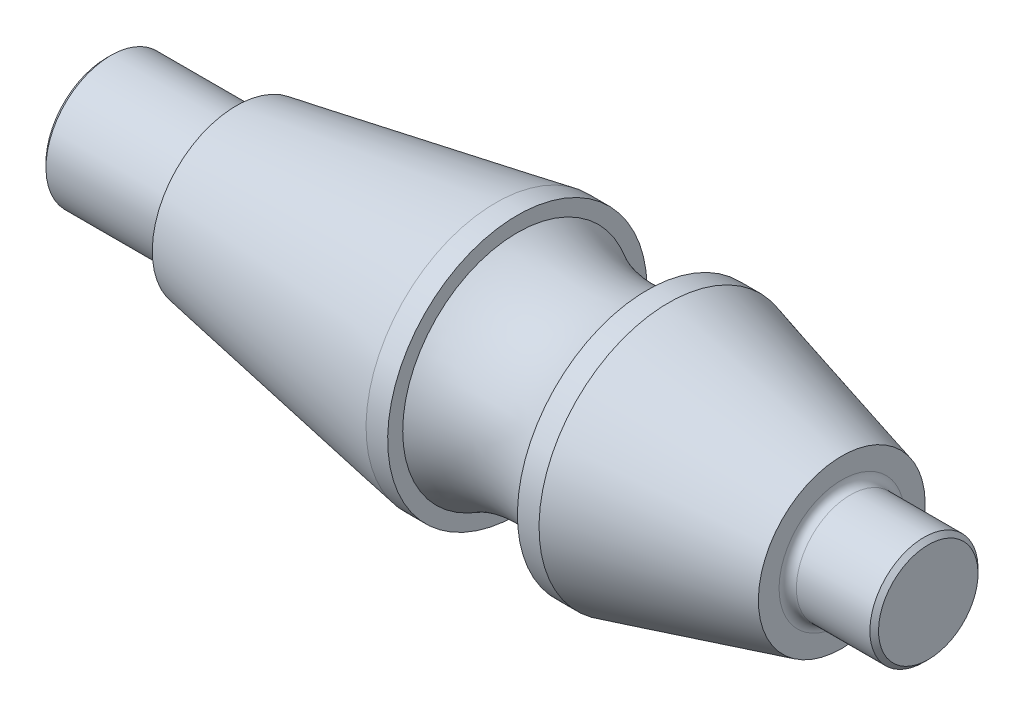
SolidWorks part; units mm, degrees
material "AISI 1045 Aço, trefilado"
ref_plane "Plano frontal" through (0, 0, 0) normal (0, 0, 1) x (1, 0, 0)
ref_plane "Plano superior" through (0, 0, 0) normal (0, 1, 0) x (1, 0, 0)
ref_plane "Plano direito" through (0, 0, 0) normal (1, 0, 0) x (0, 0, -1)
sketch "Esboço1" plane through (0, 0, 0) normal (0, 0, 1) x (1, 0, 0)
  line L0 (-95, 0) -> (95, 0) construction
  line L1 (-95, 0) -> (-95, 15)
  line L2 (-95, 15) -> (-65, 15)
  line L3 (-65, 15) -> (-65, 19.4204)
  line L4 (-65, 19.4204) -> (-5, 30)
  line L5 (-5, 30) -> (0, 30)
  line L6 (35, 30) -> (75, 19.282)
  line L7 (75, 19.282) -> (75, 12.5)
  line L8 (75, 12.5) -> (95, 12.5)
  line L9 (95, 12.5) -> (95, 0)
  line L10 (0, 30) -> (0, 26.5192)
  line L11 (30, 30) -> (30, 26.5192)
  line L12 (30, 30) -> (35, 30)
  line L13 (-95, 0) -> (95, 0)
  arc A0 (0, 26.5192) -> (30, 26.5192) centre (15, 52.5) ccw
  point P2 (0, 0)
  point P17 (0, 0)
  dimension "D11" = 45
  dimension "D12" = 30
  dimension "D1" = 190
  dimension "D2" = 30
  dimension "D3" = 25
  dimension "D4" = 30
  dimension "D5" = 20
  dimension "D6" = 10
  dimension "D7" = 15
  dimension "D8" = 60
  dimension "D9" = 90
  dimension "D10" = 60
revolve "Revolução1" add sketch "Esboço1" angle 360 about L0
chamfer "Chanfro1" distance 1 angle 45 2 edges at (-95, -15, 0) (95, -12.5, 0)
fillet "Filete1" radius 2 2 edges at (75, -12.5, 0) (-65, -15, 0)
hole_wizard "Furo roscado de M101" positions "Esboço2" profile "Esboço3" tap size "M10" standard "ISO"
sketch "Esboço2" plane through (-95, 0, 0) normal (-1, 0, 0) x (0, 0, 1)
  point P0 (0, 0)
sketch "Esboço3" plane through (-95, 0, 0) normal (0, 1, 0) x (0, 0, 1)
  line L0 (0, 0) -> (0, 17.5537)
  line L1 (0, 17.5537) -> (4.25, 15)
  line L2 (4.25, 15) -> (4.25, 0.775)
  line L3 (4.25, 0.775) -> (5.025, 0)
  line L5 (5.025, 0) -> (0, 0)
  line L6 (-4.25, 0.775) -> (-5.025, 0) construction
  line L10 (0, 17.5537) -> (-4.25, 15) construction
  line L11 (0, -6.35) -> (0, 107.95) construction
  dimension "Tap Drill Dia." = 8.5
  dimension "Tap Drill Depth" = 15
  dimension "Near C'Sink Dia." = 10.05
  dimension "Near C'Sink Angle" = 90
  dimension "Drill Angle" = 118
cosmetic thread "Rosca de furo1" parameters "D1"=20, "D2"=10
